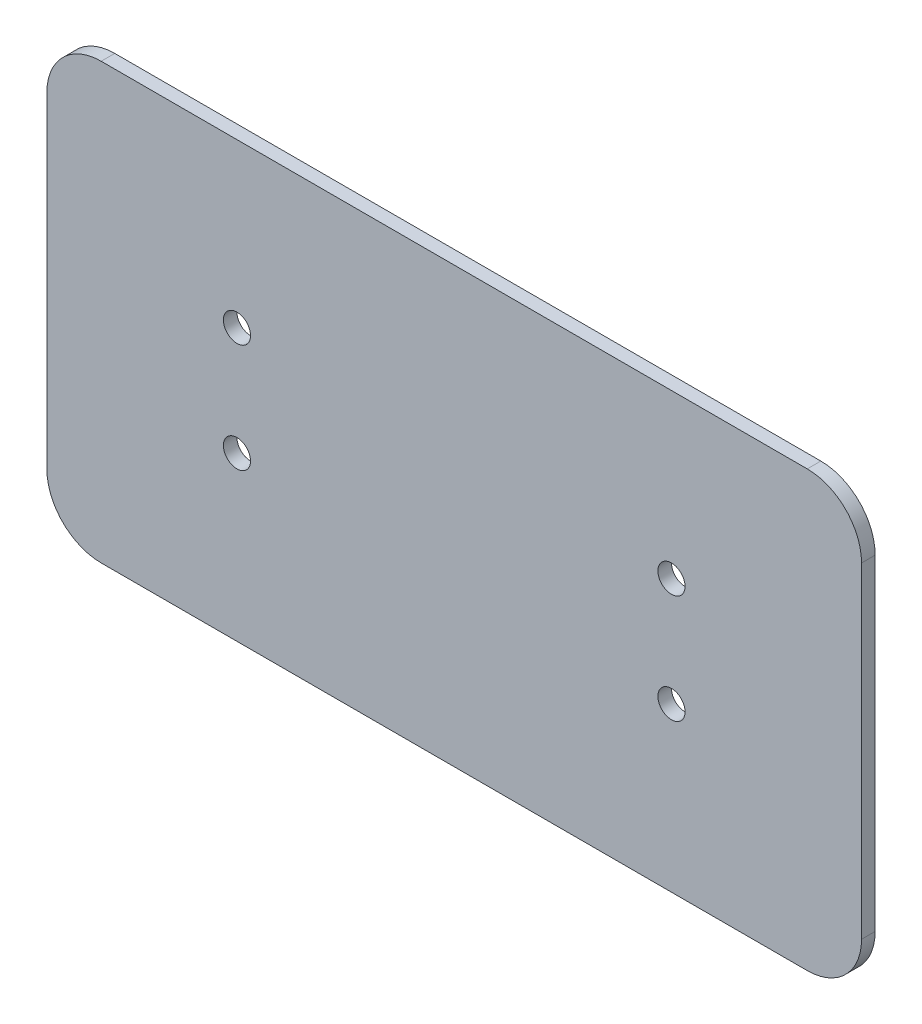
SolidWorks part; units mm, degrees
ref_plane "Front Plane" through (0, 0, 0) normal (0, 0, 1) x (1, 0, 0)
ref_plane "Top Plane" through (0, 0, 0) normal (0, 1, 0) x (1, 0, 0)
ref_plane "Right Plane" through (0, 0, 0) normal (1, 0, 0) x (0, 0, -1)
sketch "Sketch1" plane through (0, 0, 0) normal (0, 0, 1) x (1, 0, 0)
  line L0 (334.9306, -309.2543) -> (429.3841, -309.2543) construction
  line L1 (334.9306, -309.2543) -> (429.3841, -309.2543)
  line L2 (327.9293, -242.8587) -> (327.9293, -268.2587) construction
  line L3 (296.1793, -204.7587) -> (461.2793, -204.7587)
  line L4 (283.4793, -217.4587) -> (283.4793, -293.6587)
  line L5 (296.1793, -306.3587) -> (461.2793, -306.3587)
  line L6 (473.9793, -217.4587) -> (473.9793, -293.6587)
  line L7 (327.9293, -268.2587) -> (327.9293, -255.5587) construction
  line L8 (327.9293, -255.5587) -> (429.5293, -255.5587) construction
  line L9 (429.5293, -255.5587) -> (429.5293, -242.8587) construction
  line L10 (283.4793, -255.5587) -> (473.9793, -255.5587) construction
  line L11 (378.7293, -204.7587) -> (378.7293, -306.3587) construction
  circle A0 centre (429.5293, -268.2587) radius 3.175 construction
  circle A1 centre (429.5293, -242.8587) radius 3.175 construction
  circle A2 centre (327.9293, -242.8587) radius 3.175 construction
  circle A3 centre (327.9293, -268.2587) radius 3.175 construction
  circle A4 centre (429.5293, -268.2587) radius 3.175
  circle A5 centre (429.5293, -242.8587) radius 3.175
  circle A6 centre (327.9293, -242.8587) radius 3.175
  circle A7 centre (327.9293, -268.2587) radius 3.175
  arc A8 (283.4793, -293.6587) -> (296.1793, -306.3587) centre (296.1793, -293.6587) ccw
  arc A9 (461.2793, -306.3587) -> (473.9793, -293.6587) centre (461.2793, -293.6587) ccw
  arc A10 (461.2793, -204.7587) -> (473.9793, -217.4587) centre (461.2793, -217.4587) cw
  arc A11 (296.1793, -204.7587) -> (283.4793, -217.4587) centre (296.1793, -217.4587) ccw
  point P22 (378.7293, -255.5587)
  point P27 (283.4793, -306.3587)
  point P32 (473.9793, -204.7587)
  point P35 (283.4793, -204.7587)
  dimension "D3" = 12.7
  dimension "D1" = 101.6
  dimension "D2" = 190.5
extrude "Boss-Extrude1" add sketch "Sketch1" along normal blind 3.175 contours L3 A11 L4 A8 L5 A9 L6 A10 A4 A5 A6 A7
